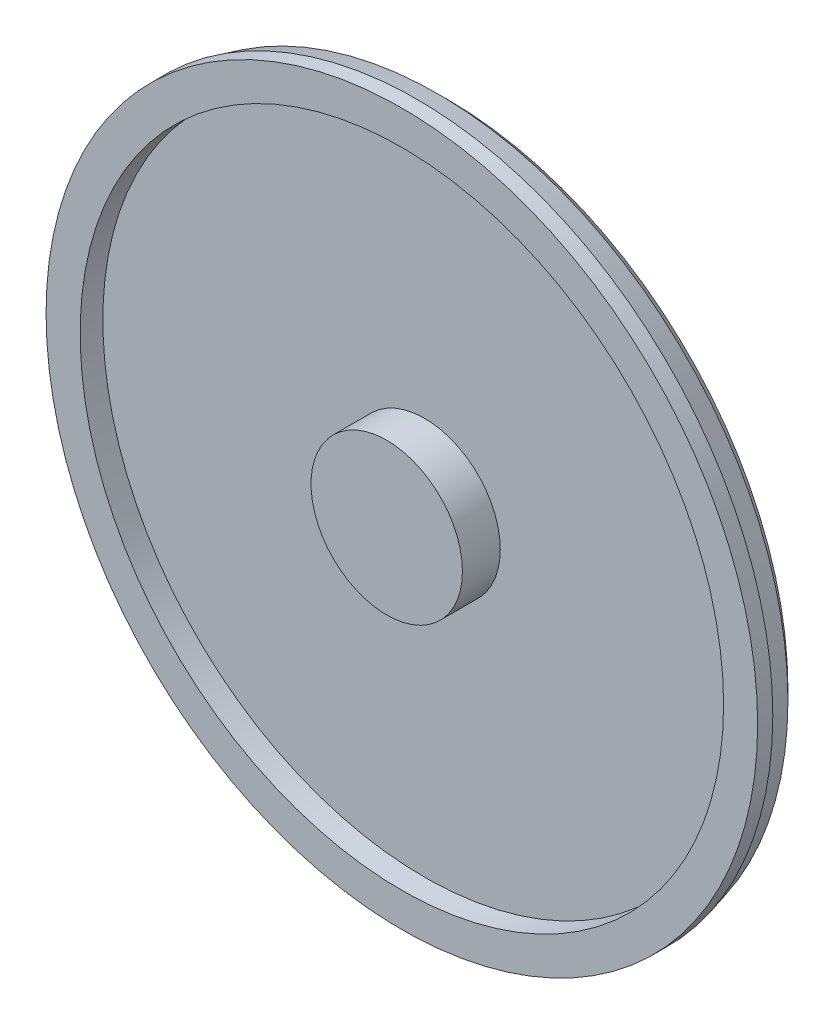
SolidWorks part; units mm, degrees
material "1060 Alloy"
ref_plane "Front Plane" through (0, 0, 0) normal (0, 0, 1) x (1, 0, 0)
ref_plane "Top Plane" through (0, 0, 0) normal (0, 1, 0) x (1, 0, 0)
ref_plane "Right Plane" through (0, 0, 0) normal (1, 0, 0) x (0, 0, -1)
sketch "Sketch2" plane through (0, 0, 0) normal (0, 0, 1) x (1, 0, 0)
  circle A0 centre (0, 0) radius 470
  dimension "D1" = 940
extrude "Boss-Extrude1" add sketch "Sketch2" along normal blind 60
sketch "Sketch3" plane through (0, 0, 60) normal (0, 0, 1) x (1, 0, 0)
  circle A0 centre (0, 0) radius 100
  dimension "D1" = 200
extrude "Boss-Extrude2" add sketch "Sketch3" along normal blind 80 from surface at -60 starting at face at (470, 0, 0)
sketch "Sketch4" plane through (0, 0, 60) normal (0, 0, 1) x (1, 0, 0)
  circle A0 centre (0, 0) radius 425
  circle A1 centre (0, 0) radius 470 construction
  circle A2 centre (0, 0) radius 470
  circle M3 centre (0, 0) radius 100
  dimension "D1" = 45
extrude "Cut-Extrude2" cut sketch "Sketch4" against normal offset from surface (30 mm away) 30 contours A0 M3 up to face at (470, 0, 0)
chamfer "Chamfer2" distance 20 angle 45 1 edges at (470, 0, 0)
chamfer "Chamfer8" distance 20 angle 15 1 edges at (470, 0, 20)
sketch "Sketch6" plane through (0, 0, 30) normal (0, 0, 1) x (1, 0, 0)
  line L0 (0, 470) -> (0, -763.3183) construction
  line L1 (281.3798, 304.221) -> (82.4484, 67.1437)
  line L2 (20, 413.9142) -> (20, 104.4318)
  line L5 (66.2231, 86.6872) -> (227.0444, 278.3466)
  line L6 (106.4513, 23.8388) -> (352.8439, 67.2845)
  line L7 (411.0989, 52.1793) -> (106.3182, -1.5618)
  line L8 (96.8697, -50.164) -> (313.5437, -175.2608)
  line L9 (348.4602, -224.2776) -> (80.4406, -69.5364)
  line L10 (41.9618, -100.6945) -> (127.533, -335.7996)
  line L11 (122.7732, -395.7926) -> (16.9239, -104.9742)
  line L12 (-32.5806, -104.1089) -> (-118.1518, -339.214)
  line L13 (-160.3609, -382.1118) -> (-54.5116, -91.2934)
  line L14 (-91.8781, -58.8097) -> (-308.5521, -183.9065)
  line L15 (-368.4602, -189.6366) -> (-100.4406, -34.8954)
  line L16 (-108.1849, 14.0073) -> (-354.5774, 57.453)
  line L17 (-404.153, 91.5716) -> (-99.3723, 37.8306)
  line L18 (-73.8707, 80.2701) -> (-234.692, 271.9295)
  line L19 (-250.7381, 329.9325) -> (-51.8066, 92.8552)
  line L20 (-4.9916, 108.9736) -> (-4.9916, 359.1672)
  circle A0 centre (0, 0) radius 470 construction
  circle A1 centre (0, 0) radius 425 construction
  circle A2 centre (0, 0) radius 100 construction
  circle A3 centre (0, 0) radius 100 construction
  circle A4 centre (0, 0) radius 425 construction
  circle A5 centre (0, 0) radius 425
  arc A7 (66.2231, 86.6872) -> (54.4415, 84.0038) centre (58.5627, 93.1151) cw
  arc A8 (20, 104.4318) -> (25.8788, 95.3205) centre (30, 104.4318) ccw
  arc A9 (20, 413.9142) -> (33.5857, 423.2493) centre (30, 413.9142) cw
  arc A10 (227.0444, 278.3466) -> (202.5957, 372.9241) centre (181.0818, 316.9139) ccw
  arc A11 (82.4484, 67.1437) -> (81.0952, 56.3852) centre (90.1088, 60.7158) ccw
  arc A12 (106.4513, 23.8388) -> (95.7012, 29.3563) centre (104.7148, 33.6869) cw
  arc A13 (352.8439, 67.2845) -> (394.9083, 155.4504) centre (342.425, 126.373) ccw
  arc A14 (281.3798, 304.221) -> (297.7875, 302.6393) centre (289.0403, 297.7931) cw
  arc A15 (106.3182, -1.5618) -> (98.3662, -8.9334) centre (108.0547, -11.4098) ccw
  arc A16 (96.8697, -50.164) -> (92.1812, -39.0273) centre (101.8697, -41.5037) cw
  arc A17 (313.5437, -175.2608) -> (402.4389, -134.7603) centre (343.5437, -123.2992) ccw
  arc A18 (411.0989, 52.1793) -> (422.6513, 40.421) centre (412.8354, 42.3312) cw
  arc A19 (80.4406, -69.5364) -> (69.6106, -70.072) centre (75.4406, -78.1967) ccw
  arc A20 (41.9618, -100.6945) -> (45.5286, -89.1496) centre (51.3587, -97.2743) cw
  arc A21 (127.533, -335.7996) -> (221.6639, -361.9151) centre (183.9146, -315.2783) ccw
  arc A22 (348.4602, -224.2776) -> (349.7518, -240.7107) centre (343.4602, -232.9379) cw
  arc A23 (16.9239, -104.9742) -> (8.2834, -98.4231) centre (7.527, -108.3944) ccw
  arc A24 (-32.5806, -104.1089) -> (-22.4273, -97.5578) centre (-23.1837, -107.5291) cw
  arc A25 (-118.1518, -339.214) -> (-62.8302, -419.7259) centre (-61.7703, -359.7352) ccw
  arc A26 (122.7732, -395.7926) -> (113.1996, -409.2112) centre (113.3762, -399.2128) cw
  arc A27 (-54.5116, -91.2934) -> (-56.9197, -80.7209) centre (-63.9086, -87.8732) ccw
  arc A28 (-91.8781, -58.8097) -> (-79.8892, -60.3176) centre (-86.8781, -67.4699) cw
  arc A29 (-308.5521, -183.9065) -> (-317.9253, -281.1422) centre (-278.5521, -235.868) ccw
  arc A30 (-160.3609, -382.1118) -> (-176.32, -386.2373) centre (-169.7578, -378.6916) cw
  arc A31 (-100.4406, -34.8954) -> (-95.4894, -25.2485) centre (-105.4406, -26.2351) ccw
  arc A32 (-108.1849, 14.0073) -> (-99.9701, 5.1458) centre (-109.9213, 4.1592) cw
  arc A33 (-354.5774, 57.453) -> (-424.2596, -11.009) centre (-364.9963, -1.6355) ccw
  arc A34 (-368.4602, -189.6366) -> (-383.3375, -182.5386) centre (-373.4602, -180.9764) cw
  arc A35 (-99.3723, 37.8306) -> (-89.3786, 42.0379) centre (-97.6358, 47.6786) ccw
  arc A36 (-73.8707, 80.2701) -> (-73.2739, 68.2015) centre (-81.5311, 73.8422) cw
  arc A37 (-234.692, 271.9295) -> (-332.0782, 264.2755) centre (-280.6547, 233.3623) ccw
  arc A38 (-404.153, 91.5716) -> (-410.9871, 106.5719) centre (-402.4165, 101.4197) cw
  arc A39 (-51.8066, 92.8552) -> (-41.4465, 89.6543) centre (-44.1461, 99.283) ccw
  arc A40 (-4.9916, 108.9736) -> (-12.292, 99.3449) centre (-14.9916, 108.9736) cw
  arc A41 (-4.9916, 359.1672) -> (-84.5137, 415.9025) centre (-64.9916, 359.1672) ccw
  arc A42 (-250.7381, 329.9325) -> (-246.3313, 345.8162) centre (-243.0776, 336.3603) cw
  point P21 (20, 424.5292)
  point P23 (60.3748, 79.7175)
  point P26 (20, 97.9796)
  point P29 (20, 424.5292)
  point P32 (269.3421, 328.755)
  point P130 (0, 0)
  dimension "D4" = 10
  dimension "D5" = 60
  dimension "D1" = 20
  dimension "D2" = 9
  dimension "D3" = 40
equation "\"A\"= 60"
equation "\"B\"= 940"
equation "\"D1@Sketch2\"=\"B\""
equation "\"D1@Boss-Extrude1\"=\"A\""
equation "\"D1@Boss-Extrude2\"=\"A\"+20"
